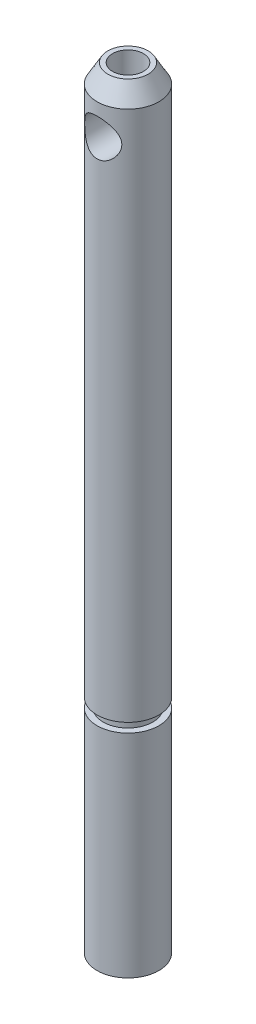
SolidWorks part; units mm, degrees
ref_plane "Front" through (0, 0, 0) normal (0, 0, 1) x (1, 0, 0)
ref_plane "Top" through (0, 0, 0) normal (0, 1, 0) x (1, 0, 0)
ref_plane "Right" through (0, 0, 0) normal (1, 0, 0) x (0, 0, -1)
sketch "Sketch3" plane through (0, 0, 0) normal (0, 1, 0) x (1, 0, 0)
  circle A0 centre (0, 0) radius 2.5
  dimension "D1" = 5
extrude "Boss-Extrude1" add sketch "Sketch3" along normal blind 62.3426
chamfer "Chamfer1" distance 1.5 angle 30 1 edges at (0, 62.3426, 2.5)
hole_wizard "M3x0.5 Tapped Hole1" positions "Sketch4" profile "Sketch5" tap size "M3x0.5" standard "ANSI Metric"
sketch "Sketch4" plane through (0, 62.3426, 0) normal (0, 1, 0) x (1, 0, 0)
  point P0 (0, 0)
cosmetic thread "Hole Thread1" parameters "D1"=4, "D2"=3
sketch "Sketch5" plane through (0, 62.3426, 0) normal (1, 0, 0) x (0, 0, 1)
  line L0 (0, 0) -> (0, 4.7511)
  line L1 (0, 4.7511) -> (1.25, 4)
  line L2 (1.25, 4) -> (1.25, 0)
  line L5 (1.25, 0) -> (0, 0)
  line L10 (0, 4.7511) -> (-1.25, 4) construction
  line L11 (0, -6.35) -> (0, 107.95) construction
  dimension "Tap Drill Dia." = 2.5
  dimension "Tap Drill Depth" = 4
  dimension "Drill Angle" = 118
cosmetic thread "Cosmetic Thread1" parameters "D1"=3.1708, "D2"=3
sketch "Sketch7" plane through (0, 0, 0) normal (0, 0, 1) x (1, 0, 0)
  line L0 (0, 62.3426) -> (0, 58.3426) construction
  line L1 (1.25, 62.3426) -> (-1.25, 62.3426) construction
  circle A0 centre (0, 58.3426) radius 1.5
  dimension "D2" = 3
  dimension "D1" = 4
extrude "Cut-Extrude1" cut sketch "Sketch7" against normal through all and the other way through all
sketch "Sketch8" plane through (0, 0, 0) normal (0, 0, 1) x (1, 0, 0)
  line L1 (-2.5, 0) -> (-1.5, 0)
  line L2 (-2.5, 0) -> (-2.5, 6)
  line L3 (-2.5, 6) -> (-1.5, 6)
  line L4 (-1.5, 0) -> (-1.5, 6)
  dimension "D1" = 6
  dimension "D2" = 1
extrude "Cut-Extrude2" cut sketch "Sketch8" against normal through all both and the other way through all
ref_plane "Plane1" through (0, 17.15, 0) normal (0, 1, 0) x (1, 0, 0)
sketch "Sketch9" plane through (0, 17.15, 0) normal (0, 1, 0) x (1, 0, 0)
  circle A0 centre (0, 0) radius 2
  circle A1 centre (0, 0) radius 3
  dimension "D1" = 4
  dimension "D2" = 6
extrude "Cut-Extrude3" cut sketch "Sketch9" along normal blind 0.75
